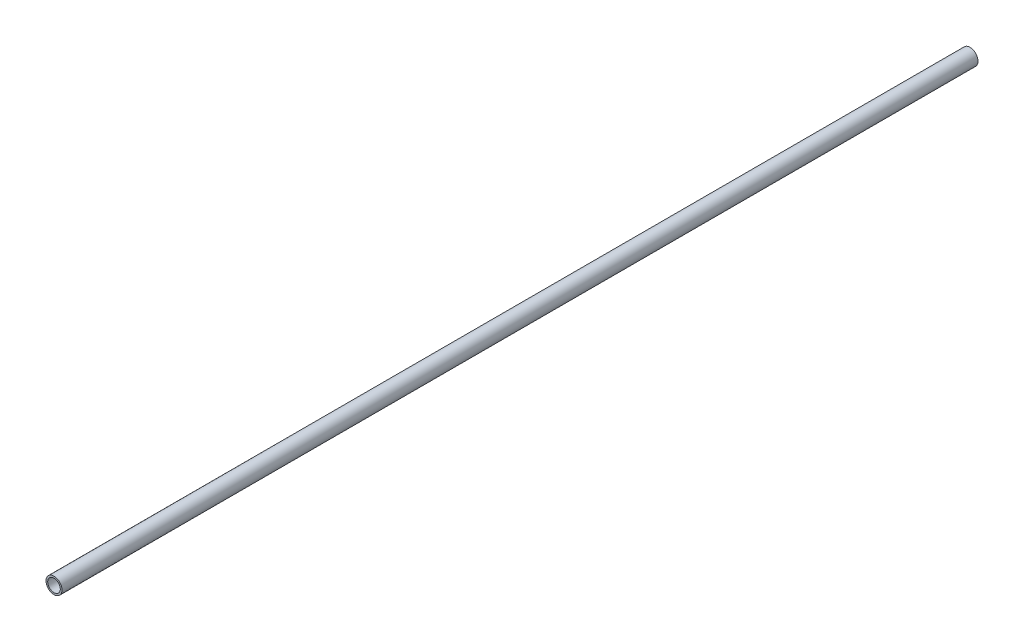
SolidWorks part; units mm, degrees
ref_plane "Front Plane" through (0, 0, 0) normal (0, 0, 1) x (1, 0, 0)
ref_plane "Top Plane" through (0, 0, 0) normal (0, 1, 0) x (1, 0, 0)
ref_plane "Right Plane" through (0, 0, 0) normal (1, 0, 0) x (0, 0, -1)
sketch "Sketch1" plane through (0, 0, 0) normal (0, 0, 1) x (1, 0, 0)
  circle A0 centre (0, 0) radius 13.335
  dimension "Pipe OD" = 26.67
extrude "Extrude-Thin1" add sketch "Sketch1" along normal mid plane 1524 thin thin type one direction reverse wall 2.8702
